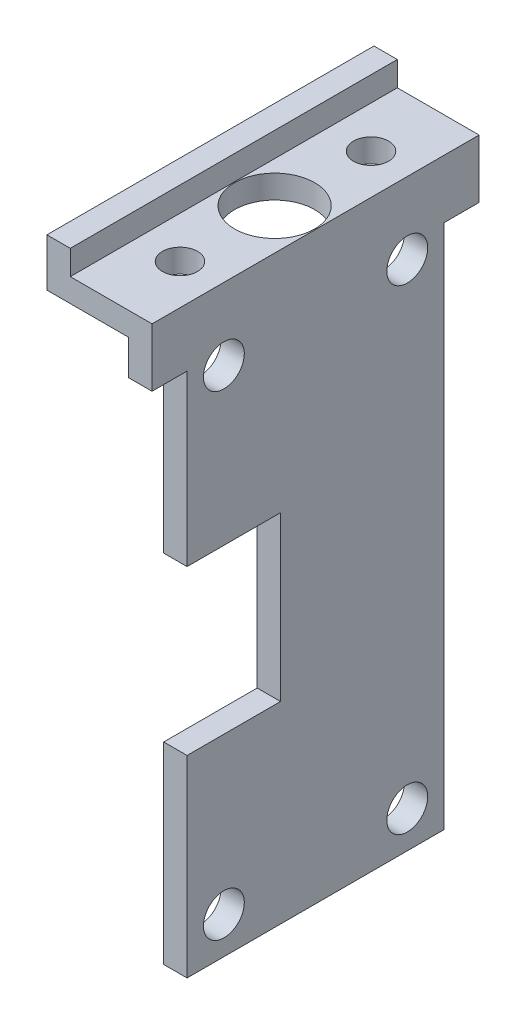
SolidWorks part; units mm, degrees
ref_plane "Front Plane" through (0, 0, 0) normal (0, 0, 1) x (1, 0, 0)
ref_plane "Top Plane" through (0, 0, 0) normal (0, 1, 0) x (1, 0, 0)
ref_plane "Right Plane" through (0, 0, 0) normal (1, 0, 0) x (0, 0, -1)
sketch "Sketch3" plane through (0, 0, 0) normal (0, 0, 1) x (1, 0, 0)
  line L0 (-16.9532, 6.6875) -> (-14.9532, 6.6875)
  line L1 (-14.9532, 6.6875) -> (-14.9532, 4.5875)
  line L2 (-14.9532, 4.5875) -> (-7.9532, 4.5875)
  line L3 (-7.9532, 4.5875) -> (-7.9532, -45.4125)
  line L4 (-7.9532, -45.4125) -> (-9.9532, -45.4125)
  line L5 (-9.9532, -45.4125) -> (-9.9532, 2.5875)
  line L6 (-9.9532, 2.5875) -> (-16.9532, 2.5875)
  line L7 (-16.9532, 2.5875) -> (-16.9532, 6.6875)
  dimension "D1" = 2
  dimension "D2" = 4.1
  dimension "D3" = 7
  dimension "D4" = 2
  dimension "D5" = 50
  dimension "D6" = 2
extrude "Boss-Extrude3" add sketch "Sketch3" along normal blind 28
sketch "Sketch4" plane through (0, 4.5875, 0) normal (0, 1, 0) x (1, 0, 0)
  line L0 (-7.9532, -28) -> (-7.9532, 0) construction
  line L1 (-7.9532, 0) -> (-14.9532, 0) construction
  line L2 (-7.9532, -28) -> (-14.9532, -28) construction
  circle A0 centre (-11.4584, -14) radius 3.43
  circle A1 centre (-11.3832, -5.822) radius 1.5
  circle A2 centre (-11.3832, -22.1777) radius 1.5
  dimension "D1" = 6.86
  dimension "D2" = 3
  dimension "D3" = 3.43
  dimension "D4" = 3
  dimension "D5" = 3.43
  dimension "D6" = 8.178
  dimension "D7" = 8.178
  dimension "D8" = 14
  dimension "D9" = 5.8223
extrude "Cut-Extrude1" cut sketch "Sketch4" against normal blind 2
sketch "Sketch6" plane through (-7.9532, 0, 0) normal (1, 0, 0) x (0, 0, -1)
  line L0 (-28, -45.4125) -> (0, -45.4125) construction
  line L1 (-28, -0.4125) -> (-25, -0.4125)
  line L2 (-28, -0.4125) -> (-28, -45.4125)
  line L3 (-28, -45.4125) -> (-25, -45.4125)
  line L4 (-25, -0.4125) -> (-25, -45.4125)
  line L6 (0, -45.4125) -> (-3, -45.4125)
  line L7 (0, -45.4125) -> (0, -0.4125)
  line L8 (0, -0.4125) -> (-3, -0.4125)
  line L9 (-3, -45.4125) -> (-3, -0.4125)
  line L10 (-28, 4.5875) -> (0, 4.5875) construction
  dimension "D1" = 22
  dimension "D2" = 3
  dimension "D3" = 5
  dimension "D4" = 5
extrude "Cut-Extrude4" cut sketch "Sketch6" against normal blind 2
sketch "Sketch7" plane through (-9.9532, 0, 0) normal (-1, 0, 0) x (0, 0, 1)
  circle A0 centre (21.85, -42.2625) radius 1.75
  circle A1 centre (6.15, -42.2625) radius 1.75
  circle A2 centre (6.15, -1.5625) radius 1.75
  circle A3 centre (21.85, -1.5625) radius 1.75
  dimension "D1" = 3.5
  dimension "D2" = 3.5
  dimension "D3" = 3.5
  dimension "D4" = 3.5
extrude "Cut-Extrude5" cut sketch "Sketch7" against normal through all
sketch "Sketch10" plane through (-7.9532, 0, 0) normal (1, 0, 0) x (0, 0, -1)
  line L0 (-25, -45.4125) -> (-25, -0.4125) construction
  line L1 (-25, -28.9125) -> (-17, -28.9125)
  line L2 (-25, -28.9125) -> (-25, -14.9125)
  line L3 (-25, -14.9125) -> (-17, -14.9125)
  line L4 (-17, -28.9125) -> (-17, -14.9125)
  line L5 (-18, -27.9125) -> (-25, -27.9125) construction
  line L6 (-25, -15.9125) -> (-18, -15.9125) construction
  line L7 (-18, -15.9125) -> (-18, -27.9125) construction
  dimension "D1" = 1
  dimension "D2" = 1
  dimension "D3" = 1
extrude "Cut-Extrude7" cut sketch "Sketch10" against normal through all
